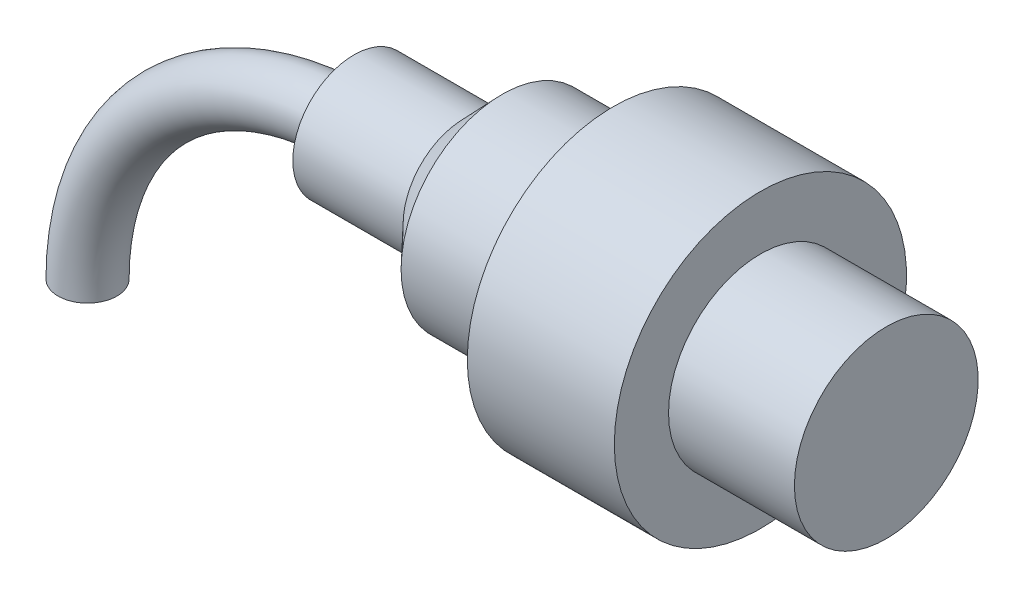
SolidWorks part; units mm, degrees
ref_plane "Front Plane" through (0, 0, 0) normal (0, 0, 1) x (1, 0, 0)
ref_plane "Top Plane" through (0, 0, 0) normal (0, 1, 0) x (1, 0, 0)
ref_plane "Right Plane" through (0, 0, 0) normal (1, 0, 0) x (0, 0, -1)
sketch "Sketch1" plane through (0, 0, 0) normal (0, 0, 1) x (1, 0, 0)
  arc A0 (0, 0) -> (28.9914, 28.9914) centre (28.9914, 0) cw
  dimension "D1" = 41
sketch "Sketch2" plane through (0, 0, 0) normal (0, 1, 0) x (1, 0, 0)
  circle A0 centre (0, 0) radius 3.2
  dimension "D1" = 6.4
sweep "Sweep1" add profiles "Sketch2" path "Sketch1"
sketch "Sketch4" plane through (0, 0, 0) normal (0, 0, 1) x (1, 0, 0)
  line L0 (28.9914, 25.7914) -> (28.9914, 32.1914) construction
  line L1 (28.9914, 28.9914) -> (28.9914, 35.6414)
  line L2 (28.9914, 28.9914) -> (40.9914, 28.9914)
  line L3 (28.9914, 35.6414) -> (40.9914, 35.6414)
  line L4 (40.9914, 28.9914) -> (40.9914, 35.6414)
  line L5 (40.9914, 35.6414) -> (45.1239, 39.9914)
  line L6 (45.1239, 39.9914) -> (55.1239, 39.9914)
  line L7 (55.1239, 39.9914) -> (55.1239, 28.9914)
  line L8 (55.1239, 28.9914) -> (40.9914, 28.9914)
  line L9 (55.1239, 39.9914) -> (57.231, 43.3914)
  line L10 (57.231, 43.3914) -> (57.231, 44.8914)
  line L11 (57.231, 44.8914) -> (73.231, 44.8914)
  line L12 (73.231, 44.8914) -> (73.231, 28.9914)
  line L13 (73.231, 28.9914) -> (55.1239, 28.9914)
  line L14 (73.231, 28.9914) -> (73.231, 38.9914)
  line L15 (73.231, 28.9914) -> (86.931, 28.9914)
  line L16 (73.231, 38.9914) -> (86.931, 38.9914)
  line L17 (86.931, 28.9914) -> (86.931, 38.9914)
  arc A0 (28.9914, 32.1914) -> (-3.2, 0) centre (28.9914, 0) ccw
  arc A1 (28.9914, 25.7914) -> (3.2, 0) centre (28.9914, 0) ccw
  arc A2 (28.9914, 25.7914) -> (3.2, 0) centre (28.9914, 0) ccw
  arc A3 (28.9914, 32.1914) -> (-3.2, 0) centre (28.9914, 0) ccw
  point P1 (28.9914, 28.9914)
  dimension "D1" = 6.65
  dimension "D2" = 12
  dimension "D3" = 11
  dimension "D4" = 6
  dimension "D5" = 10
  dimension "D6" = 4
  dimension "D7" = 16
  dimension "D8" = 15.9
  dimension "D9" = 10
  dimension "D10" = 13.7
  dimension "D11" = 1.5
revolve "Revolve1" add sketch "Sketch4" angle 360 about L2
